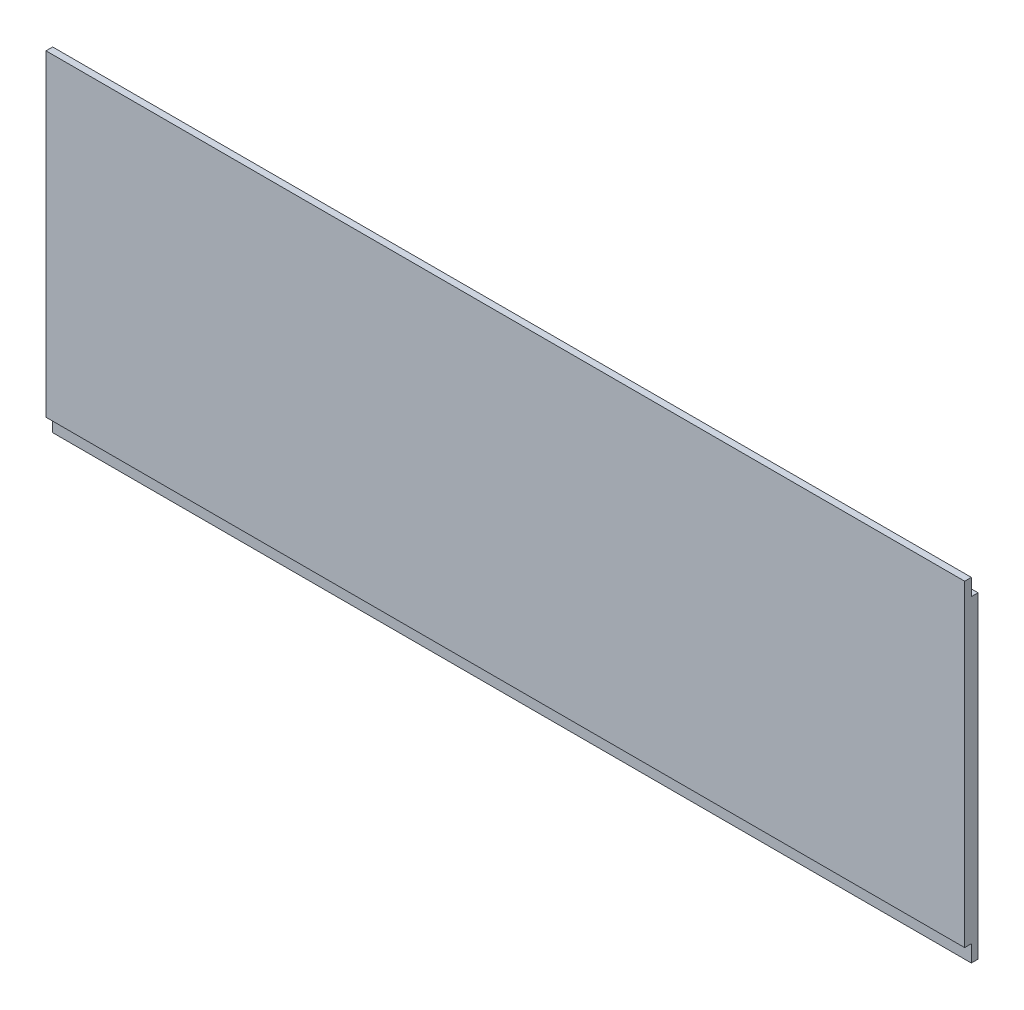
SolidWorks part; units mm, degrees
ref_plane "Спереди" through (0, 0, 0) normal (0, 0, 1) x (1, 0, 0)
ref_plane "Сверху" through (0, 0, 0) normal (0, 1, 0) x (1, 0, 0)
ref_plane "Справа" through (0, 0, 0) normal (1, 0, 0) x (0, 0, -1)
sketch "Эскиз1" plane through (0, 0, 0) normal (1, 0, 0) x (0, 0, -1)
  line L0 (0, 0) -> (0, 190)
  line L1 (0, 190) -> (-4, 190)
  line L2 (-4, 190) -> (-4, 200)
  line L3 (-4, 200) -> (-8, 200)
  line L4 (-8, 200) -> (-8, 10)
  line L5 (-8, 10) -> (-4, 10)
  line L6 (-4, 10) -> (-4, 0)
  line L7 (-4, 0) -> (0, 0)
extrude "Бобышка-Вытянуть1" add sketch "Эскиз1" along normal blind 550
